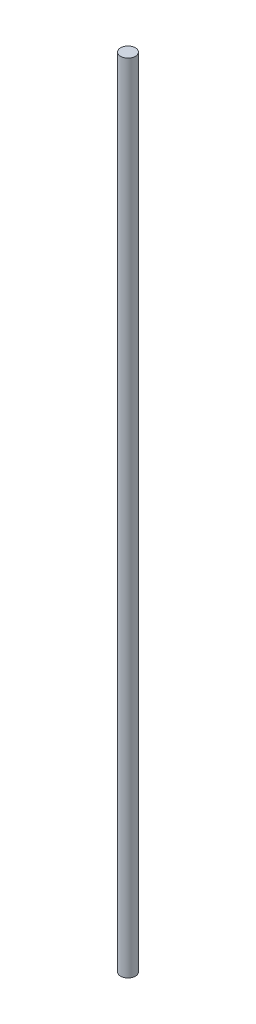
SolidWorks part; units mm, degrees
ref_plane "Front Plane" through (0, 0, 0) normal (0, 0, 1) x (1, 0, 0)
ref_plane "Top Plane" through (0, 0, 0) normal (0, 1, 0) x (1, 0, 0)
ref_plane "Right Plane" through (0, 0, 0) normal (1, 0, 0) x (0, 0, -1)
sketch "Sketch1" plane through (0, 0, 0) normal (0, 1, 0) x (1, 0, 0)
  circle A0 centre (0, 0) radius 15.875
extrude "Boss-Extrude1" add sketch "Sketch1" along normal blind 1708.15
